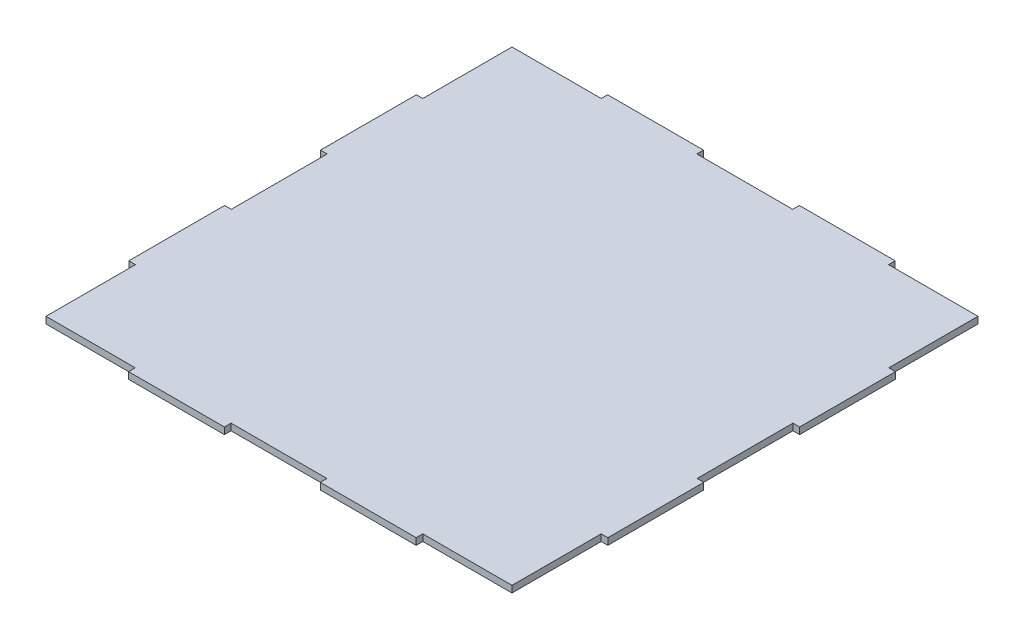
SolidWorks part; units mm, degrees
ref_plane "Front Plane" through (0, 0, 0) normal (0, 0, 1) x (1, 0, 0)
ref_plane "Top Plane" through (0, 0, 0) normal (0, 1, 0) x (1, 0, 0)
ref_plane "Right Plane" through (0, 0, 0) normal (1, 0, 0) x (0, 0, -1)
sketch "Sketch1" plane through (0, 0, 0) normal (0, 1, 0) x (1, 0, 0)
  line L1 (114.3, -114.3) -> (-114.3, -114.3)
  line L2 (114.3, -114.3) -> (114.3, 114.3)
  line L3 (114.3, 114.3) -> (-114.3, 114.3)
  line L4 (-114.3, -114.3) -> (-114.3, 114.3)
  line L5 (114.3, -114.3) -> (-114.3, 114.3) construction
  line L6 (114.3, 114.3) -> (-114.3, -114.3) construction
  point P0 (0, 0)
  dimension "D2" = 228.6
extrude "Boss-Extrude1" add sketch "Sketch1" along normal blind 3.175
sketch "Sketch3" plane through (0, 3.175, 0) normal (0, 1, 0) x (1, 0, 0)
  line L0 (-111.125, -111.125) -> (-68.58, -111.125)
  line L1 (114.3, 114.3) -> (-114.3, 114.3) construction
  line L2 (114.3, -114.3) -> (114.3, 114.3) construction
  line L3 (-114.3, -114.3) -> (-68.58, -114.3)
  line L4 (-68.58, -111.125) -> (-68.58, -114.3)
  line L5 (-114.3, -114.3) -> (114.3, -114.3) construction
  line L6 (-22.86, -114.3) -> (22.86, -114.3)
  line L7 (-22.86, -114.3) -> (-22.86, -111.125)
  line L8 (-22.86, -111.125) -> (22.86, -111.125)
  line L9 (22.86, -114.3) -> (22.86, -111.125)
  line L10 (68.4753, 111.125) -> (111.125, 111.125)
  line L11 (68.4753, 111.125) -> (68.4753, 114.3)
  line L12 (68.4753, 114.3) -> (114.3, 114.3)
  line L13 (-114.3, -68.4753) -> (-114.3, -114.3)
  line L14 (-111.125, -68.4753) -> (-114.3, -68.4753)
  line L15 (-111.125, -68.4753) -> (-111.125, -111.125)
  line L16 (114.3, 68.58) -> (111.125, 68.58)
  line L17 (-111.125, -22.7553) -> (-114.3, -22.7553)
  line L18 (-114.3, 22.9647) -> (-114.3, -22.7553)
  line L19 (-111.125, 22.9647) -> (-114.3, 22.9647)
  line L20 (-111.125, 22.9647) -> (-111.125, -22.7553)
  line L22 (111.125, 68.58) -> (111.125, 111.125)
  line L24 (-111.2297, 111.2297) -> (-111.2297, 68.6847)
  line L25 (114.3, 114.3) -> (114.3, 68.58)
  line L26 (-114.4046, 114.4047) -> (-114.4047, 68.6847)
  line L27 (-111.2297, 68.6847) -> (-114.4047, 68.6847)
  line L28 (-68.6847, 114.3) -> (-114.4046, 114.4047)
  line L29 (-68.6847, 111.2297) -> (-68.6847, 114.3)
  line L31 (-68.6847, 111.2297) -> (-111.2297, 111.2297)
  line L32 (111.125, -111.125) -> (111.125, -68.58)
  line L33 (114.3, -114.3) -> (114.3, -68.58)
  line L34 (111.125, -68.58) -> (114.3, -68.58)
  line L35 (68.58, -114.3) -> (114.3, -114.3)
  line L36 (68.58, -111.125) -> (68.58, -114.3)
  line L37 (68.58, -111.125) -> (111.125, -111.125)
  line L38 (111.125, 22.86) -> (111.125, -22.86)
  line L39 (111.125, 22.86) -> (114.3, 22.86)
  line L40 (114.3, 22.86) -> (114.3, -22.86)
  line L41 (111.125, -22.86) -> (114.3, -22.86)
  line L42 (22.7553, 114.3) -> (22.7553, 111.125)
  line L43 (-22.9647, 111.125) -> (22.7553, 111.125)
  line L44 (-22.9647, 114.3) -> (-22.9647, 111.125)
  line L45 (-22.9647, 114.3) -> (22.7553, 114.3)
  dimension "D1" = 0
  dimension "D2" = 0
  dimension "D3" = 0
  dimension "D4" = 0
  dimension "D5" = 45.72
  dimension "D6" = 45.72
  dimension "D7" = 3.175
  dimension "D8" = 0
  dimension "D9" = 45.72
  dimension "D10" = 45.72
  dimension "D11" = 45.72
  dimension "D12" = 45.72
  dimension "D13" = 45.8247
  dimension "D14" = 0
  dimension "D15" = 45.72
  dimension "D16" = 45.72
  dimension "D17" = 45.72
  dimension "D18" = 45.8247
  dimension "D19" = 45.72
  dimension "D20" = 45.72
  dimension "D21" = 45.72
  dimension "D22" = 3.175
  dimension "D23" = 45.72
  dimension "D24" = 45.72
  dimension "D25" = 45.72
  dimension "D26" = 45.72
  dimension "D27" = 45.72
  dimension "D28" = 3.175
  dimension "D29" = 45.72
extrude "Cut-Extrude1" cut sketch "Sketch3" against normal blind 6.35
sketch "Sketch4" plane through (0, 3.175, 0) normal (0, 1, 0) x (1, 0, 0)
  line L0 (79.8338, -68.1721) -> (64.5938, -68.1721)
  line L1 (64.5938, -68.1721) -> (64.5938, -58.9023)
  line L2 (-52.8189, -91.6878) -> (-52.8189, -94.9797)
  line L3 (-52.8189, -82.3609) -> (-52.8189, -79.0691)
  line L4 (-54.4648, -77.4232) -> (-89.5778, -77.4232)
  line L5 (-91.2237, -79.0691) -> (-91.2237, -94.9797)
  line L6 (-54.4648, -96.6256) -> (-89.5778, -96.6256)
  line L7 (-60.4298, -81.714) -> (-58.8936, -81.714)
  line L8 (-58.8936, -81.714) -> (-58.8936, -85.5545)
  line L9 (-58.8936, -85.5545) -> (-55.0531, -85.5545)
  line L10 (-55.0531, -85.5545) -> (-55.0531, -87.0907)
  line L11 (-55.0531, -87.0907) -> (-58.8936, -87.0907)
  line L12 (-60.4298, -81.714) -> (-60.4298, -85.5545)
  line L13 (-60.4298, -85.5545) -> (-64.2702, -85.5545)
  line L14 (-64.2702, -85.5545) -> (-64.2702, -87.0907)
  line L15 (-64.2702, -87.0907) -> (-60.4298, -87.0907)
  line L16 (-60.4298, -87.0907) -> (-60.4298, -90.9312)
  line L17 (-60.4298, -90.9312) -> (-58.8936, -90.9312)
  line L18 (79.8338, -43.4071) -> (60.7838, -43.4071)
  line L19 (60.7838, -43.4071) -> (60.7838, -71.9821)
  line L20 (60.7838, -71.9821) -> (79.8338, -71.9821)
  line L21 (79.8338, -71.9821) -> (79.8338, -68.1721)
  line L22 (64.5938, -58.9023) -> (74.082, -58.9023)
  line L23 (74.082, -58.9023) -> (74.082, -55.0923)
  line L24 (74.082, -55.0923) -> (64.5938, -55.0923)
  line L25 (64.5938, -55.0923) -> (64.5938, -48.2349)
  line L26 (79.8338, -43.4071) -> (79.8338, -47.2961)
  line L27 (-58.8936, -90.9312) -> (-58.8936, -87.0907)
  line L28 (-87.1088, -85.2761) -> (-87.1088, -86.8123)
  line L29 (-87.1088, -86.8123) -> (-77.8917, -86.8123)
  line L30 (-77.8917, -86.8123) -> (-77.8917, -85.2761)
  line L31 (-77.8917, -85.2761) -> (-87.1088, -85.2761)
  line L32 (-51.5489, -83.6309) -> (-49.903, -83.6309)
  line L33 (-48.633, -84.9009) -> (-48.633, -89.1478)
  line L34 (-49.903, -90.4178) -> (-51.5489, -90.4178)
  line L35 (-24.7088, 57.4509) -> (-23.8231, 54.9254)
  line L36 (27.0057, 52.9506) -> (8.4927, 52.8787)
  line L37 (-33.6312, 54.6473) -> (-23.8231, 54.6473)
  line L38 (-25.5756, 54.8757) -> (-35.562, 63.8326)
  line L39 (79.8338, -47.2961) -> (64.5938, -47.2961)
  line L40 (64.5938, -47.2961) -> (64.5938, -48.2349)
  line L41 (-71.9312, -47.2961) -> (-71.9312, -48.2349)
  line L42 (-71.9312, -68.1721) -> (-71.9312, -58.9023)
  line L43 (-75.7412, -43.4071) -> (-75.7412, -71.9821)
  line L44 (-71.9312, -71.9821) -> (-71.9312, -68.1721)
  line L45 (-62.443, -58.9023) -> (-62.443, -55.0923)
  line L46 (-71.9312, -55.0923) -> (-71.9312, -48.2349)
  line L47 (-56.6912, -47.2961) -> (-71.9312, -47.2961)
  line L48 (-56.6912, -43.4071) -> (-75.7412, -43.4071)
  line L49 (-75.7412, -71.9821) -> (-71.9312, -71.9821)
  line L50 (-71.9312, -58.9023) -> (-62.443, -58.9023)
  line L51 (-62.443, -55.0923) -> (-71.9312, -55.0923)
  line L52 (-56.6912, -43.4071) -> (-56.6912, -47.2961)
  line L53 (-35.562, 63.8326) -> (-38.2979, 63.8326)
  line L54 (-38.2979, 63.8326) -> (-38.2979, 62.4009)
  line L55 (-12.1561, 74.8666) -> (-12.1561, 80.194)
  line L56 (-37.2829, 62.4009) -> (-28.6178, 54.7198)
  line L57 (-23.8231, 54.6473) -> (-23.8231, 54.9254)
  line L58 (17.885, 42.1519) -> (-39.1011, 42.1519)
  line L59 (49.2532, 28.0699) -> (47.6511, 27.564)
  line L60 (-41.2257, 33.9725) -> (39.1344, 33.9725)
  line L61 (-33.6312, 44.039) -> (10.6851, 44.039)
  line L62 (-48.5618, 27.6483) -> (-50.164, 28.4072)
  line L63 (10.6851, 44.039) -> (10.6851, 49.4797)
  line L64 (-39.2019, 36.2493) -> (-39.1011, 42.1519)
  line L65 (40.3055, 31.9488) -> (-39.9642, 31.9488)
  line L66 (-32.6034, 6.823) -> (-33.5298, 6.0417)
  line L67 (31.5869, 6.6824) -> (32.5355, 5.9282)
  line L68 (42.3425, 17.361) -> (43.2911, 16.6068)
  line L69 (19.9014, 5.3916) -> (19.9014, 4.1796)
  line L70 (19.9014, 4.1796) -> (15.1884, 4.1796)
  line L71 (12.4616, 5.3916) -> (15.1884, 5.3916)
  line L72 (12.4624, 5.3328) -> (12.4624, 4.1209)
  line L73 (12.4624, 4.1209) -> (7.7494, 4.1209)
  line L74 (7.7494, 4.1209) -> (7.7494, 5.3328)
  line L75 (-33.6312, 54.6473) -> (-33.6312, 44.039)
  line L76 (10.6851, 49.4797) -> (27.0094, 49.4797)
  line L77 (-38.2979, 62.4009) -> (-37.2829, 62.4009)
  line L78 (-33.5298, 6.0417) -> (-36.8624, 9.3742)
  line L79 (-36.8624, 9.3742) -> (-36.0054, 10.2312)
  line L80 (5.0226, 5.3328) -> (7.7494, 5.3328)
  line L81 (4.9827, 5.3267) -> (4.9827, 4.1148)
  line L82 (4.9827, 4.1148) -> (0.2697, 4.1148)
  line L83 (0.2697, 4.1148) -> (0.2697, 5.3267)
  line L84 (-2.4571, 5.3267) -> (0.2697, 5.3267)
  line L85 (-2.4456, 5.3149) -> (-2.4456, 4.103)
  line L86 (-2.4456, 4.103) -> (-7.1586, 4.103)
  line L87 (-7.1586, 4.103) -> (-7.1586, 5.3149)
  line L88 (-9.8854, 5.3149) -> (-7.1586, 5.3149)
  line L89 (-9.849, 5.2892) -> (-9.849, 4.0773)
  line L90 (-9.849, 4.0773) -> (-14.562, 4.0773)
  line L91 (-14.562, 4.0773) -> (-14.562, 5.2892)
  line L92 (-17.2888, 5.2892) -> (-14.562, 5.2892)
  line L93 (-17.3078, 5.272) -> (-17.3078, 4.0601)
  line L94 (-17.3078, 4.0601) -> (-22.0208, 4.0601)
  line L95 (-22.0208, 4.0601) -> (-22.0208, 5.272)
  line L96 (-24.7476, 5.272) -> (-22.0208, 5.272)
  line L97 (-24.7793, 5.2897) -> (-24.7793, 4.0778)
  line L98 (-24.7793, 4.0778) -> (-29.4922, 4.0778)
  line L99 (-29.4922, 4.0778) -> (-29.4922, 5.2897)
  line L100 (27.3996, 5.3408) -> (27.3996, 4.1289)
  line L101 (27.3996, 4.1289) -> (22.6866, 4.1289)
  line L102 (22.6866, 4.1289) -> (22.6866, 5.3408)
  line L103 (19.9598, 5.3408) -> (22.6866, 5.3408)
  line L104 (35.8197, 9.3764) -> (34.9627, 10.2333)
  line L105 (34.9627, 10.2333) -> (36.8909, 12.1615)
  line L106 (36.9524, 12.0267) -> (37.9011, 11.2726)
  line L107 (37.9011, 11.2726) -> (41.2337, 14.6052)
  line L108 (41.2337, 14.6052) -> (40.3767, 15.4621)
  line L109 (40.3767, 15.4621) -> (42.3049, 17.3902)
  line L110 (43.2911, 16.6068) -> (46.6335, 19.9296)
  line L111 (46.6335, 19.9296) -> (45.7791, 20.7891)
  line L112 (-37.9853, 12.178) -> (-36.0572, 10.2499)
  line L113 (-37.9853, 12.178) -> (-38.9117, 11.3967)
  line L114 (-38.9117, 11.3967) -> (-42.2443, 14.7293)
  line L115 (-42.2443, 14.7293) -> (-41.3874, 15.5862)
  line L116 (-41.3874, 15.5862) -> (-43.3155, 17.5143)
  line L117 (-43.3706, 17.5554) -> (-44.297, 16.7741)
  line L118 (-44.297, 16.7741) -> (-47.6296, 20.1067)
  line L119 (-47.6296, 20.1067) -> (-46.7726, 20.9636)
  line L120 (45.2242, 41.7719) -> (45.9853, 42.7244)
  line L121 (53.2956, 65.0386) -> (56.1142, 65.3252)
  line L122 (37.4227, 62.5603) -> (44.2926, 67.3973)
  line L123 (69.2702, 72.2617) -> (69.4266, 72.8163)
  line L124 (46.3304, 59.5305) -> (48.4427, 57.8769)
  line L125 (46.1371, 44.6606) -> (54.7341, 37.8665)
  line L126 (39.2455, 44.0577) -> (45.996, 39.4461)
  line L127 (69.4266, 72.8163) -> (69.9812, 72.6599)
  line L128 (69.1233, 31.4498) -> (69.1514, 30.8743)
  line L129 (58.5887, 68.6051) -> (64.3514, 71.8322)
  line L130 (67.9463, 71.4502) -> (68.012, 72.0241)
  line L131 (56.1337, 38.6591) -> (58.2325, 37.4474)
  line L132 (58.5944, 35.3665) -> (64.3144, 32.0642)
  line L133 (69.9812, 72.6599) -> (70.1271, 73.1771)
  line L134 (67.9721, 31.8242) -> (68.6124, 31.9958)
  line L135 (67.914, 32.399) -> (67.9721, 31.8242)
  line L136 (69.999, 30.9158) -> (70.0719, 30.6436)
  line L137 (68.65, 71.8442) -> (68.7156, 72.4182)
  line L138 (70.1271, 73.1771) -> (69.0884, 75.0319)
  line L139 (53.2419, 35.4746) -> (65.8702, 28.1837)
  line L140 (50.4297, 38.9466) -> (45.996, 39.4461)
  line L141 (44.1021, 61.2861) -> (40.4426, 59.7881)
  line L142 (68.012, 72.0241) -> (68.65, 71.8442)
  line L143 (27.0112, 47.8471) -> (27.003, 55.4193)
  line L144 (48.4427, 57.8769) -> (48.4427, 51.8929)
  line L145 (64.3144, 32.0642) -> (67.1691, 32.8291)
  line L146 (56.1142, 65.3252) -> (58.1995, 66.5292)
  line L147 (48.4427, 51.8929) -> (48.4427, 45.4303)
  line L148 (68.7156, 72.4182) -> (69.2702, 72.2617)
  line L149 (67.1691, 32.8291) -> (67.2737, 32.2274)
  line L150 (39.6497, 59.8658) -> (46.0424, 64.3667)
  line L151 (47.08, 43.9154) -> (48.4427, 45.4303)
  line L152 (55.9816, 70.1052) -> (44.843, 67.6014)
  line L153 (67.1958, 71.0299) -> (67.3084, 71.6301)
  line L154 (45.1136, 43.4209) -> (53.701, 36.5591)
  line L155 (64.3514, 71.8322) -> (67.1958, 71.0299)
  line L156 (27.003, 55.4193) -> (29.5268, 56.3493)
  line L157 (67.2737, 32.2274) -> (67.914, 32.399)
  line L158 (58.1995, 66.5292) -> (58.5887, 68.6051)
  line L159 (45.0625, 60.618) -> (53.6499, 67.4799)
  line L160 (53.3319, 38.9747) -> (56.1337, 38.6591)
  line L161 (65.8702, 28.1837) -> (69.009, 28.8026)
  line L162 (46.0924, 59.3425) -> (54.7226, 66.1589)
  line L163 (37.4738, 41.4786) -> (44.3284, 36.6199)
  line L164 (55.9816, 70.1052) -> (65.958, 75.6919)
  line L165 (67.3084, 71.6301) -> (67.9463, 71.4502)
  line L166 (46.0424, 64.3667) -> (50.9433, 65.3172)
  line L167 (58.2325, 37.4474) -> (58.5944, 35.3665)
  line L168 (69.1514, 30.8743) -> (69.999, 30.9158)
  line L169 (68.5477, 31.4217) -> (69.1233, 31.4498)
  line L170 (27.0112, 47.8471) -> (29.4822, 46.7237)
  line L171 (44.1021, 61.2861) -> (45.0625, 60.618)
  line L172 (65.958, 75.6919) -> (69.0884, 75.0319)
  line L173 (68.6124, 31.9958) -> (68.5477, 31.4217)
  line L174 (45.2242, 41.7719) -> (39.4538, 43.9154)
  line L175 (70.0719, 30.6436) -> (69.009, 28.8026)
  line L176 (53.2419, 35.4746) -> (44.8818, 36.4163)
  line L177 (15.1884, 4.1796) -> (15.1884, 5.3916)
  line L178 (32.4871, 6.0438) -> (35.8197, 9.3764)
  line L179 (81.4093, -81.714) -> (81.4093, -85.5545)
  line L180 (53.1941, -85.2761) -> (53.1941, -86.8123)
  line L181 (85.2498, -85.5545) -> (85.2498, -87.0907)
  line L182 (62.4112, -86.8123) -> (62.4112, -85.2761)
  line L183 (87.484, -82.3609) -> (87.484, -79.0691)
  line L184 (87.484, -91.6878) -> (87.484, -94.9797)
  line L185 (88.754, -83.6309) -> (90.3999, -83.6309)
  line L186 (91.6699, -84.9009) -> (91.6699, -89.1478)
  line L187 (79.8731, -81.714) -> (79.8731, -85.5545)
  line L188 (76.0326, -85.5545) -> (76.0326, -87.0907)
  line L189 (49.0792, -79.0691) -> (49.0792, -94.9797)
  line L190 (79.8731, -87.0907) -> (79.8731, -90.9312)
  line L191 (79.8731, -81.714) -> (81.4093, -81.714)
  line L192 (81.4093, -90.9312) -> (81.4093, -87.0907)
  line L193 (81.4093, -85.5545) -> (85.2498, -85.5545)
  line L194 (53.1941, -86.8123) -> (62.4112, -86.8123)
  line L195 (85.2498, -87.0907) -> (81.4093, -87.0907)
  line L196 (90.3999, -90.4178) -> (88.754, -90.4178)
  line L197 (62.4112, -85.2761) -> (53.1941, -85.2761)
  line L198 (79.8731, -85.5545) -> (76.0326, -85.5545)
  line L199 (85.8381, -77.4232) -> (50.7251, -77.4232)
  line L200 (76.0326, -87.0907) -> (79.8731, -87.0907)
  line L201 (85.8381, -96.6256) -> (50.7251, -96.6256)
  line L202 (79.8731, -90.9312) -> (81.4093, -90.9312)
  arc A0 (-54.4648, -96.6256) -> (-52.8189, -94.9797) centre (-54.4648, -94.9797) ccw
  arc A1 (-52.8189, -79.0691) -> (-54.4648, -77.4232) centre (-54.4648, -79.0691) ccw
  arc A2 (-89.5778, -77.4232) -> (-91.2237, -79.0691) centre (-89.5778, -79.0691) ccw
  arc A3 (-89.5778, -96.6256) -> (-91.2237, -94.9797) centre (-89.5778, -94.9797) cw
  arc A4 (-51.5489, -83.6309) -> (-52.8189, -82.3609) centre (-51.5489, -82.3609) cw
  arc A5 (-52.8189, -91.6878) -> (-51.5489, -90.4178) centre (-51.5489, -91.6878) cw
  arc A6 (-48.633, -89.1478) -> (-49.903, -90.4178) centre (-49.903, -89.1478) cw
  arc A7 (-48.633, -84.9009) -> (-49.903, -83.6309) centre (-49.903, -84.9009) ccw
  circle A8 centre (3.2396, 80.194) radius 1.3602
  arc A9 (-31.6873, 94.1353) -> (-27.5763, 91.3471) centre (-27.7251, 95.5525) ccw
  arc A10 (-31.6873, 94.1353) -> (-31.2881, 95.2918) centre (-30.7665, 94.4646) cw
  arc A11 (32.1636, 50.4819) -> (31.1707, 49.8298) centre (34.5343, 45.7907) ccw
  arc A12 (34.59, 51.0525) -> (33.4072, 50.9428) centre (34.4808, 45.7974) ccw
  arc A13 (37.7131, 54.1296) -> (36.7135, 53.4878) centre (34.3917, 58.2034) cw
  arc A14 (39.6511, 46.3711) -> (39.4184, 47.536) centre (34.4134, 45.9304) ccw
  arc A15 (46.1371, 44.6606) -> (45.1136, 43.4209) centre (44.4929, 44.9757) ccw
  arc A16 (38.8301, 48.7245) -> (38.0777, 49.6438) centre (34.4124, 45.8765) ccw
  arc A17 (30.8298, 54.5182) -> (37.4227, 62.5603) centre (34.5345, 58.2046) cw
  arc A18 (39.2212, 56.1141) -> (38.6399, 55.0782) centre (34.376, 58.1518) cw
  arc A19 (35.4498, 53.0853) -> (34.2659, 52.9879) centre (34.4297, 58.2415) cw
  arc A20 (46.0924, 59.3425) -> (45.0625, 60.618) centre (44.4418, 59.0633) cw
  arc A21 (30.2891, 48.8391) -> (37.4738, 41.4786) centre (34.547, 45.8085) ccw
  arc A22 (32.9612, 53.2258) -> (31.8701, 53.6956) centre (34.4812, 58.2574) cw
  arc A23 (39.2455, 44.0577) -> (39.6125, 45.0454) centre (34.5189, 46.3764) ccw
  arc A24 (44.2926, 67.3973) -> (46.0424, 64.3667) centre (45.1675, 65.882) cw
  arc A25 (37.0003, 50.4171) -> (35.9044, 50.8756) centre (34.4367, 45.8284) ccw
  arc A26 (39.6211, 58.5744) -> (39.5942, 57.3868) centre (34.3864, 58.0989) cw
  circle A27 centre (34.4808, 45.7974) radius 1.3595
  arc A28 (45.996, 39.4461) -> (44.3284, 36.6199) centre (44.6832, 38.3157) cw
  arc A29 (54.7341, 37.8665) -> (53.701, 36.5591) centre (55.2638, 36.3861) cw
  circle A30 centre (34.4297, 58.2415) radius 1.3595
  arc A31 (54.7226, 66.1589) -> (53.6499, 67.4799) centre (55.2127, 67.6529) ccw
  arc A32 (50.7251, -77.4232) -> (49.0792, -79.0691) centre (50.7251, -79.0691) ccw
  arc A33 (50.7251, -96.6256) -> (49.0792, -94.9797) centre (50.7251, -94.9797) cw
  arc A34 (87.484, -79.0691) -> (85.8381, -77.4232) centre (85.8381, -79.0691) ccw
  arc A35 (87.484, -91.6878) -> (88.754, -90.4178) centre (88.754, -91.6878) cw
  arc A36 (91.6699, -84.9009) -> (90.3999, -83.6309) centre (90.3999, -84.9009) ccw
  arc A37 (85.8381, -96.6256) -> (87.484, -94.9797) centre (85.8381, -94.9797) ccw
  arc A38 (88.754, -83.6309) -> (87.484, -82.3609) centre (88.754, -82.3609) cw
  arc A39 (91.6699, -89.1478) -> (90.3999, -90.4178) centre (90.3999, -89.1478) cw
  spline S0 degree 3 poles (-17.9193, 104.3826) (-16.1801, 103.3549) (-13.8659, 102.9504) (-12.7018, 101.2995) (-9.3809, 96.5898) (-7.4843, 91.0226) (-4.8755, 85.8841) knots 0 0 0 0 1 1 1 2 2 2 2
  spline S1 degree 3 poles (-4.8755, 85.8841) (-3.6414, 84.7106) (-1.2397, 84.4766) (1.1673, 84.2876) (1.9383, 84.0922) knots 0 0 0 0 0.660166 1 1 1 1
  spline S2 degree 2 poles (1.9383, 84.0922) (23.9746, 74.9198) (1.9541, 62.6047) knots 0 0 0 1 1 1
  spline S3 degree 3 poles (8.3841, 52.807) (9.0233, 53.171) (8.8743, 55.1171) (8.8871, 57.4) (7.0581, 58.8348) (5.3319, 59.9237) (3.6967, 60.908) (1.8522, 61.0391) (0.6824, 62.0814) (1.9541, 62.6047) knots 0 0 0 0 0.149981 0.334602 0.472667 0.600784 0.774924 0.851697 1 1 1 1
  spline S4 degree 2 poles (40.3055, 31.9488) (45.9779, 30.583) (46.5743, 25.4025) knots 0 0 0 1 1 1
  spline S5 degree 2 poles (27.3996, 5.3408) (29.8422, 4.7974) (31.5869, 6.6824) knots 0 0 0 1 1 1
  spline S6 degree 2 poles (-29.4922, 5.2897) (-31.3346, 5.4535) (-32.6034, 6.823) knots 0 0 0 1 1 1
  spline S7 degree 3 poles (-24.7088, 57.4509) (-22.861, 64.3862) (-18.2143, 70.9512) (-12.1561, 74.8666) knots 0 0 0 0 1 1 1 1
  spline S8 degree 3 poles (-12.1561, 80.194) (-16.2643, 83.3662) (-21.4422, 91.5641) (-27.5763, 91.3471) knots 0 0 0 0 0.93874 0.93874 0.93874 0.93874
  spline S9 degree 3 poles (-31.2881, 95.2918) (-28.8514, 95.8471) (-23.813, 95.6304) (-19.4284, 93.4488) (-17.386, 92.3249) knots 0 0 0 0 0.517057 1 1 1 1
  spline S10 degree 3 poles (17.885, 42.1519) (20.1055, 40.0438) (21.6169, 36.7178) (24.5465, 35.8276) (30.2332, 34.0998) (37.723, 37.3161) (43.4349, 34.3098) (43.9134, 34.058) (44.4371, 33.8768) (44.8684, 33.5509) (45.7102, 32.9149) (46.4995, 32.2046) (47.2295, 31.4428) (48.4398, 30.1799) (49.0854, 29.5806) (49.2532, 28.0699) knots 0 0 0 0 1 1 1 2 2 2 3 3 3 4 4 4 5 5 5 5
  spline S11 degree 3 poles (47.6511, 27.564) (47.439, 27.8821) (47.1622, 28.1573) (46.9765, 28.4915) (46.9202, 28.5928) (46.9485, 28.7275) (46.8922, 28.8288) (46.8048, 28.9861) (46.6838, 29.1249) (46.5549, 29.2504) (45.6146, 30.166) (44.6406, 31.0462) (43.6879, 31.9488) (43.5725, 32.0581) (43.4854, 32.2018) (43.3506, 32.2861) (43.2523, 32.3475) (43.1146, 32.3141) (43.0133, 32.3704) (42.856, 32.4578) (42.749, 32.6203) (42.5917, 32.7077) (41.5592, 33.2813) (40.2841, 33.6851) (39.1344, 33.9725) knots 0 0 0 0 1 1 1 2 2 2 3 3 3 4 4 4 5 5 5 6 6 6 7 7 7 8 8 8 8
  spline S12 degree 3 poles (-39.2019, 36.2493) (-44.0546, 36.5867) (-49.009, 33.2444) (-50.164, 28.4072) knots 0 0 0 0 1 1 1 1
  spline S13 degree 3 poles (-48.5618, 27.6483) (-47.9988, 31.0312) (-44.7084, 34.0452) (-41.2257, 33.9725) knots 0 0 0 0 1 1 1 1
  spline S14 degree 2 poles (46.5743, 25.4025) (47.1508, 23.0089) (45.7791, 20.7891) knots 0 0 0 1 1 1
  spline S15 degree 3 poles (-39.9642, 31.9488) (-45.2189, 32.1131) (-49.6107, 25.5806) (-46.7726, 20.9636) knots 0 0 0 0 1 1 1 1
  spline S16 degree 3 poles (-17.9193, 104.3826) (-19.122, 104.723) (-19.4088, 102.2188) (-19.0525, 101.7187) knots 0 0 0 0 1 1 1 1
  spline S17 degree 1 poles (-19.0525, 101.7187) (-15.3081, 95.5015) knots 0 0 1 1
  spline S18 degree 3 poles (-15.3081, 95.5015) (-12.9185, 90.0872) (-15.0427, 92.0441) (-17.1006, 92.323) (-17.386, 92.3249) knots 0 0 0 0 0.860377 1 1 1 1
  spline S19 degree 2 poles (37.7131, 54.1296) (40.2857, 52.5674) (38.6399, 55.0782) knots 0 0 0 1 1 1
  spline S20 degree 2 poles (30.8298, 54.5182) (29.5452, 51.7964) (31.8701, 53.6956) knots 0 0 0 1 1 1
  spline S21 degree 2 poles (32.9612, 53.2258) (33.1047, 50.2195) (34.2659, 52.9879) knots 0 0 0 1 1 1
  spline S22 degree 2 poles (39.6211, 58.5744) (42.3547, 59.8337) (39.3529, 59.8732) knots 0 0 0 1 1 1
  spline S23 degree 2 poles (39.2212, 56.1141) (42.226, 55.9426) (39.5942, 57.3868) knots 0 0 0 1 1 1
  spline S24 degree 2 poles (32.1636, 50.4819) (31.7829, 53.4675) (33.4072, 50.9428) knots 0 0 0 1 1 1
  spline S25 degree 2 poles (37.0003, 50.4171) (39.2625, 52.4022) (38.0777, 49.6438) knots 0 0 0 1 1 1
  spline S26 degree 2 poles (34.59, 51.0525) (35.6555, 53.8673) (35.9044, 50.8756) knots 0 0 0 1 1 1
  spline S27 degree 2 poles (38.8301, 48.7245) (41.7595, 49.4153) (39.4184, 47.536) knots 0 0 0 1 1 1
  spline S28 degree 2 poles (30.2891, 48.8391) (28.5513, 51.2964) (31.1707, 49.8298) knots 0 0 0 1 1 1
  spline S29 degree 2 poles (35.4498, 53.0853) (36.9879, 50.4983) (36.7135, 53.4878) knots 0 0 0 1 1 1
  spline S30 degree 2 poles (39.6511, 46.3711) (42.5619, 45.6057) (39.6125, 45.0454) knots 0 0 0 1 1 1
  point P22 (-68.8938, -100.376)
  point P332 (34.3522, 58.3843)
  point P333 (34.4512, 58.1323)
  point P336 (34.5023, 45.9067)
  point P337 (34.4033, 45.6547)
  point P359 (71.4091, -100.376)
  dimension "D2" = 1.27
equation "\"SideLength\"= .75 * 12"
equation "\"D2@Sketch1\" = \"SideLength\""
equation "\"D5@Sketch3\"=\"SideLength\"/5"
equation "\"D6@Sketch3\"=\"SideLength\"/5"
equation "\"thick\"=0.125"
equation "\"D7@Sketch3\"=\"thick\""
